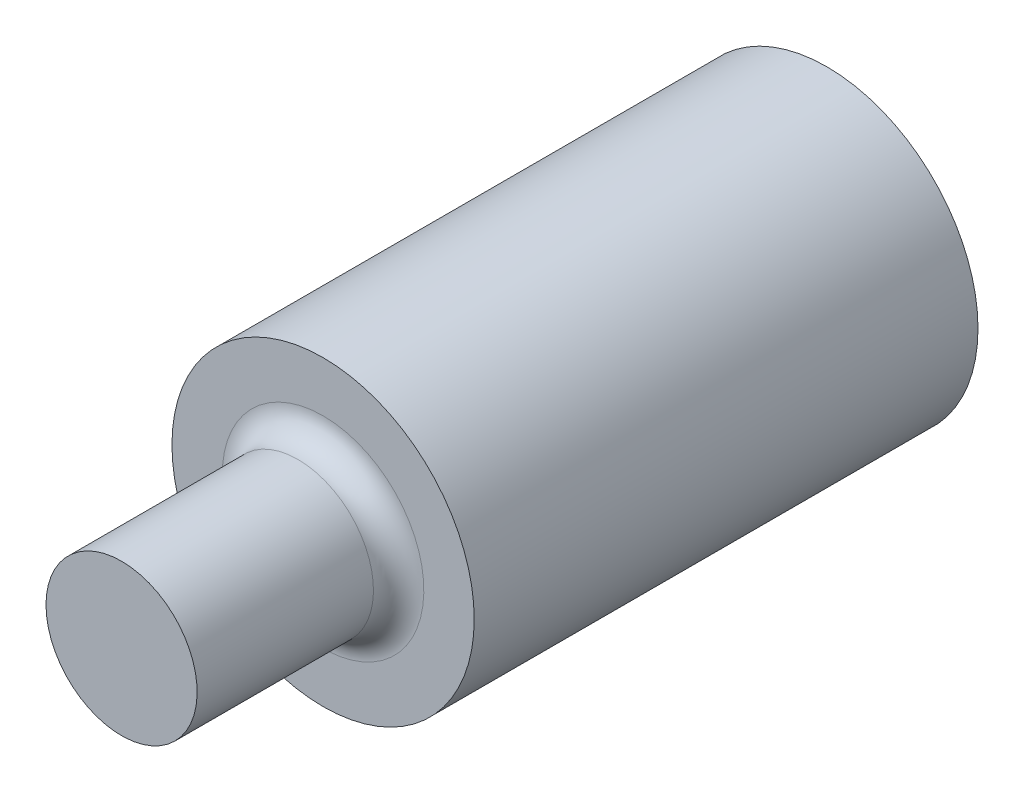
SolidWorks part; units mm, degrees
ref_plane "Front Plane" through (0, 0, 0) normal (0, 0, 1) x (1, 0, 0)
ref_plane "Top Plane" through (0, 0, 0) normal (0, 1, 0) x (1, 0, 0)
ref_plane "Right Plane" through (0, 0, 0) normal (1, 0, 0) x (0, 0, -1)
sketch "Sketch1" plane through (0, 0, 0) normal (1, 0, 0) x (0, 0, -1)
  line L0 (29, 0) -> (-29, 0) construction
  line L1 (29, 0) -> (34, 0) construction
  line L2 (-29, 0.75) -> (-29, -0.75) construction
  line L3 (34, 1.5) -> (34, -1.5) construction
  line L4 (34, 1.5) -> (29, 1.5) construction
  point P4 (0, 0)
  point P9 (-29, 0)
  point P12 (34, 0)
  dimension "Length" = 63
  dimension "Head Height" = 5
  dimension "Head Diameter" = 3
  dimension "Diameter" = 1.5
sketch "Sketch2" plane through (0, 0, 0) normal (1, 0, 0) x (0, 0, -1)
  line L0 (-29, 0.75) -> (28.75, 0.75)
  line L1 (29, 1) -> (29, 1.5)
  line L2 (29, 1.5) -> (34, 1.5)
  line L3 (34, 1.5) -> (34, 0)
  line L4 (34, 0) -> (-29, 0)
  line L5 (-29, 0) -> (-29, 0.75)
  arc A0 (28.75, 0.75) -> (29, 1) centre (28.75, 1) ccw
  dimension "D1" = 0.25
revolve "Revolve1" add sketch "Sketch2" angle 360 about L4
sketch "Sketch3" plane through (0, 0, 0) normal (1, 0, 0) x (0, 0, -1)
  line L0 (34, -1.5) -> (34, 1.5) construction
  line L1 (27, 1.6913) -> (-48, 1.6913)
  line L2 (27, 1.6913) -> (27, -1.8214)
  line L3 (27, -1.8214) -> (-48, -1.8214)
  line L4 (-48, 1.6913) -> (-48, -1.8214)
  line L5 (1.65, 0) -> (-1.65, 0) construction
  dimension "D1" = 7
  dimension "D2" = 75
  dimension "D3" = 3.5128
  dimension "D4" = 1.6913
extrude "Cut-Extrude1" cut sketch "Sketch3" against normal through all and the other way through all
